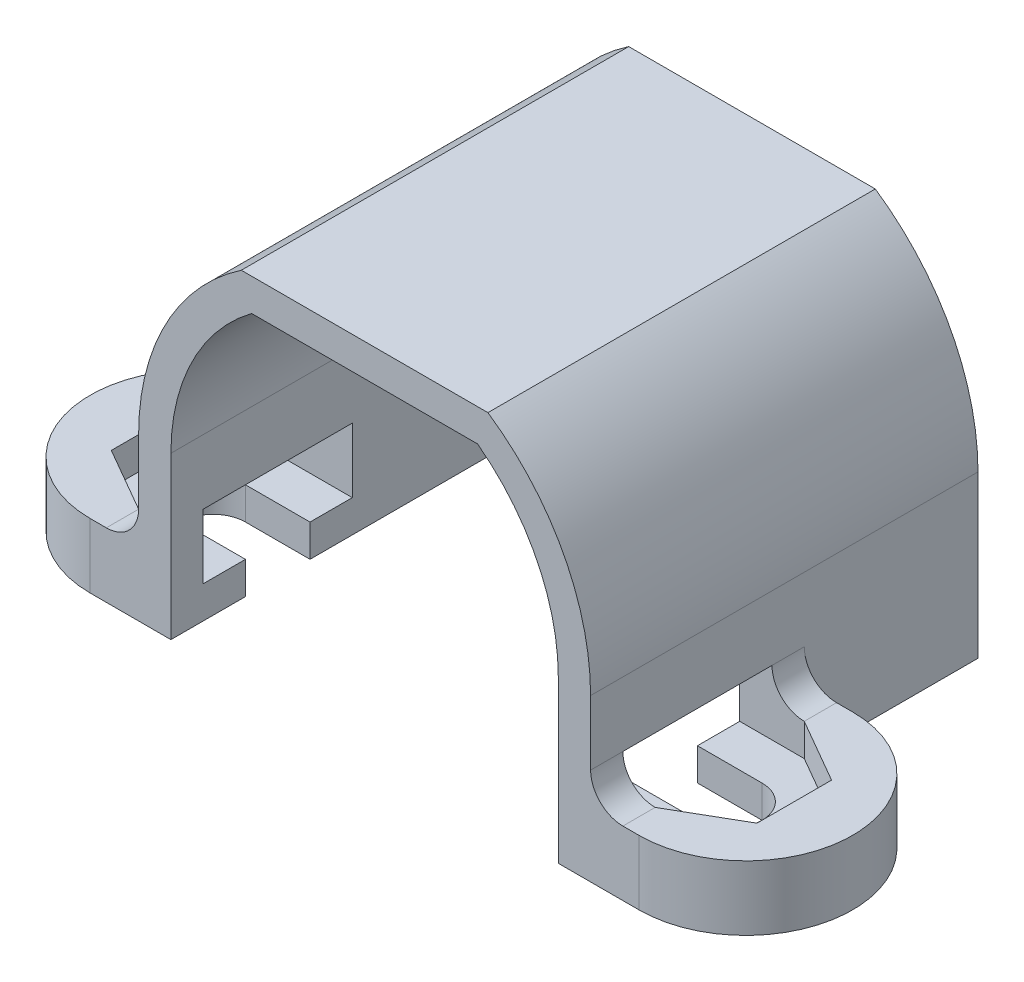
SolidWorks part; units mm, degrees
ref_plane "Front Plane" through (0, 0, 0) normal (0, 0, 1) x (1, 0, 0)
ref_plane "Top Plane" through (0, 0, 0) normal (0, 1, 0) x (1, 0, 0)
ref_plane "Right Plane" through (0, 0, 0) normal (1, 0, 0) x (0, 0, -1)
sketch "Sketch1" plane through (0, 0, 0) normal (0, 0, 1) x (1, 0, 0)
  line L1 (3.5, 10) -> (-3.5, 10)
  line L2 (-6, 5) -> (-6, 0)
  line L3 (-6, 0) -> (-7, 0)
  line L4 (6, 5) -> (6, 0)
  line L5 (6, 0) -> (7, 0)
  line L7 (7, 5) -> (7, 1)
  line L8 (3.8197, 11) -> (-3.8197, 11)
  line L9 (-7, 5) -> (-7, 1)
  line L13 (-7, 1) -> (-7, 0)
  line L14 (7, 1) -> (7, 0)
  line L15 (-6, 0) -> (-12.5, 0) construction
  line L16 (6, 0) -> (12.5, 0) construction
  line L17 (-7, 1) -> (-12.5, 1) construction
  line L18 (7, 1) -> (12.5, 1) construction
  arc A0 (-3.5, 10) -> (-6, 5) centre (0.25, 5) ccw
  arc A1 (6, 5) -> (3.5, 10) centre (-0.25, 5) ccw
  arc A2 (7, 5) -> (3.8197, 11) centre (-0.25, 5) ccw
  arc A3 (-3.8197, 11) -> (-7, 5) centre (0.25, 5) ccw
  dimension "D2" = 6.25
  dimension "D1" = 1
extrude "Boss-Extrude1" add sketch "Sketch1" against normal blind 12
sketch "Sketch4" plane through (0, 0, 0) normal (0, -1, 0) x (1, 0, 0)
  line L1 (-8.5, -1) -> (-10.5, -2.1547) construction
  line L2 (-7, 0) -> (-6, 0) construction
  line L3 (6, 0) -> (3.5, 0) construction
  line L4 (-7, 0) -> (-8.5, 0)
  line L5 (8.5, 0) -> (7, 0)
  line L7 (-8.5, -6.6188) -> (-7, -6.6188)
  line L8 (-7, -12) -> (-7, 0) construction
  line L9 (8.5, -6.6188) -> (7, -6.6188)
  line L10 (7, -12) -> (7, 0) construction
  line L11 (7, 0) -> (7, -6.6188)
  line L12 (-7, 0) -> (-7, -6.6188)
  line L13 (-10.5, -2.1547) -> (-10.5, -4.4641) construction
  line L14 (-10.5, -4.4641) -> (-8.5, -5.6188) construction
  line L15 (-8.5, -5.6188) -> (-6.5, -4.4641) construction
  line L16 (-6.5, -4.4641) -> (-6.5, -2.1547) construction
  line L17 (-6.5, -2.1547) -> (-8.5, -1) construction
  arc A0 (-8.5, 0) -> (-8.5, -6.6188) centre (-8.5, -3.3094) ccw
  arc A1 (8.5, -6.6188) -> (8.5, 0) centre (8.5, -3.3094) ccw
  circle A2 centre (-8.5, -3.3094) radius 2 construction
  line M6 (7, -12) -> (7, 0)
  dimension "D1" = 4
  dimension "D3" = 3.3094
  dimension "D2" = 1
extrude "Boss-Extrude3" add sketch "Sketch4" against normal blind 2 contours L4 A0 L7 L12 | L9 A1 L5 M6
sketch "Sketch5" plane through (0, 2, 0) normal (0, 1, 0) x (1, 0, 0)
  line L16 (-7, 4.3094) -> (-8, 4.3094)
  line L18 (-8, 2.3094) -> (-7, 2.3094)
  line L19 (-8, 5.6188) -> (-10, 4.4641) construction
  line L20 (-10, 4.4641) -> (-10, 2.1547) construction
  line L21 (-10, 2.1547) -> (-8, 1) construction
  line L22 (-8, 1) -> (-6, 2.1547) construction
  line L23 (-6, 2.1547) -> (-6, 4.4641) construction
  line L24 (-6, 4.4641) -> (-8, 5.6188) construction
  line L25 (-7, 0) -> (-7, 6.6188) construction
  line L30 (0, 0) -> (0, 12) construction
  line L31 (3.8197, 12) -> (-3.8197, 12) construction
  line L45 (-7, 4.3094) -> (-3.8197, 4.3094)
  line L46 (-3.8197, 12) -> (-3.8197, 0) construction
  line L47 (-3.8197, 4.3094) -> (-3.8197, 2.3094)
  line L48 (-3.8197, 2.3094) -> (-7, 2.3094)
  line L49 (6, 4.4641) -> (8, 5.6188) construction
  line L50 (6, 2.1547) -> (6, 4.4641) construction
  line L51 (8, 1) -> (6, 2.1547) construction
  line L52 (10, 2.1547) -> (8, 1) construction
  line L53 (10, 4.4641) -> (10, 2.1547) construction
  line L54 (8, 5.6188) -> (10, 4.4641) construction
  line L55 (3.8197, 2.3094) -> (7, 2.3094)
  line L56 (3.8197, 4.3094) -> (3.8197, 2.3094)
  line L57 (7, 4.3094) -> (3.8197, 4.3094)
  line L58 (8, 2.3094) -> (7, 2.3094)
  line L59 (7, 4.3094) -> (8, 4.3094)
  arc A4 (-8.5, 6.6188) -> (-8.5, 0) centre (-8.5, 3.3094) ccw construction
  circle A5 centre (-8, 3.3094) radius 2 construction
  arc A8 (-8, 4.3094) -> (-8, 2.3094) centre (-8, 3.3094) ccw
  circle A9 centre (8, 3.3094) radius 2 construction
  arc A11 (8, 2.3094) -> (8, 4.3094) centre (8, 3.3094) ccw
  point P27 (-11.8094, 3.3094)
  dimension "D3" = 4
fillet "Fillet2" radius 1 2 edges at (7, 2, -3.3094) (-7, 2, -3.3094)
extrude "Cut-Extrude7" cut sketch "Sketch5" against normal blind 3
sketch "Sketch6" plane through (0, 2, 0) normal (0, 1, 0) x (1, 0, 0)
  line L0 (-8, 2.3094) -> (-8, 4.3094) construction
  line L1 (-8, 5.6188) -> (-10, 4.4641)
  line L2 (-10, 4.4641) -> (-10, 2.1547)
  line L3 (-10, 2.1547) -> (-8, 1)
  line L7 (-8, 5.6188) -> (-6, 5.6188)
  line L8 (-6, 5.6188) -> (-6, 1)
  line L9 (-6, 1) -> (-8, 1)
  line L10 (0, 0) -> (0, 12) construction
  line L11 (-6, 4.4641) -> (-8, 5.6188) [skipped]
  line L12 (-8, 1) -> (-6, 2.1547) [skipped]
  line L13 (-6, 2.1547) -> (-6, 4.4641) [skipped]
  line L14 (3.8197, 12) -> (-3.8197, 12) construction
  line L15 (6, 1) -> (8, 1)
  line L16 (6, 5.6188) -> (6, 1)
  line L17 (8, 5.6188) -> (6, 5.6188)
  line L18 (10, 2.1547) -> (8, 1)
  line L19 (10, 4.4641) -> (10, 2.1547)
  line L20 (8, 5.6188) -> (10, 4.4641)
  circle A0 centre (-8, 3.3094) radius 2 construction
  circle A1 centre (8, 3.3094) radius 2 construction
  dimension "D1" = 4
extrude "Cut-Extrude8" cut sketch "Sketch6" against normal blind 1 and the other way blind 1
